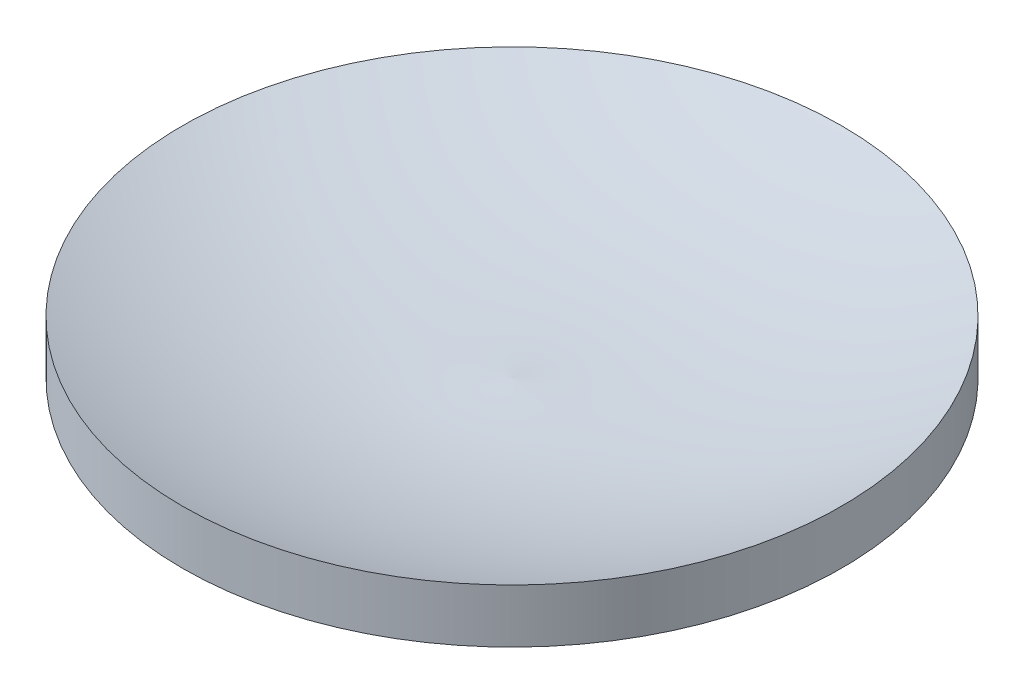
SolidWorks part; units mm, degrees
material "Glass"
ref_plane "Front Plane" through (0, 0, 0) normal (0, 0, 1) x (1, 0, 0)
ref_plane "Top Plane" through (0, 0, 0) normal (0, 1, 0) x (1, 0, 0)
ref_plane "Right Plane" through (0, 0, 0) normal (1, 0, 0) x (0, 0, -1)
sketch "Sketch1" plane through (0, 0, 0) normal (1, 0, 0) x (0, 0, -1)
  line L2 (49, 8) -> (49, 16)
  line L3 (0, 0) -> (0, 8)
  arc A0 (0, 0) -> (49, 8) centre (0, 154.0625) ccw
  arc A1 (0, 8) -> (49, 16) centre (7.8536, 113.9593) ccw
  dimension "D1" = 49
  dimension "D2" = 8
  dimension "D3" = 8
  dimension "D4" = 16
revolve "Revolve1" add sketch "Sketch1" angle 360 about L3
